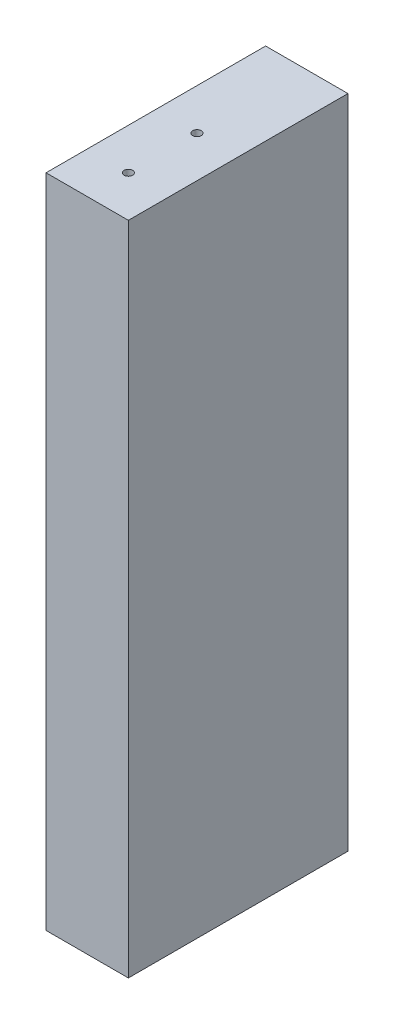
SolidWorks part; units mm, degrees
material "MDF"
ref_plane "Front" through (0, 0, 0) normal (0, 0, 1) x (1, 0, 0)
ref_plane "Top" through (0, 0, 0) normal (0, 1, 0) x (1, 0, 0)
ref_plane "Right" through (0, 0, 0) normal (1, 0, 0) x (0, 0, -1)
sketch "Sketch1" plane through (0, 0, 0) normal (0, 0, 1) x (1, 0, 0)
  line L0 (487.3718, 6450.33) -> (273.05, 6450.33) construction
  line L1 (461.9718, 6450.33) -> (442.9218, 6450.33)
  line L2 (461.9718, 6450.33) -> (461.9718, 6602.1458)
  line L3 (461.9718, 6602.1458) -> (442.9218, 6602.1458)
  line L4 (442.9218, 6450.33) -> (442.9218, 6602.1458)
  line L5 (493.1812, 6602.1458) -> (273.05, 6602.1458) construction
  dimension "D1" = 25.4
  dimension "D2" = 19.05
extrude "Boss-Extrude1" add sketch "Sketch1" along normal blind 50.8
hole_wizard "5/64 (0.07813) Diameter Hole1" positions "Sketch2" profile "Sketch3" hole size "5/64" standard "ANSI Inch"
sketch "Sketch2" plane through (5.6155, 0, -19.05) normal (0, 0, -1) x (-1, 0, 0)
  point P0 (-481.5892, 6993.255)
  point P9 (-386.3392, 6993.255)
  point P18 (-291.0892, 6993.255)
  point P21 (-295.275, 6965.1359)
  point P33 (-295.275, 6812.7359)
  point P45 (-295.275, 6660.3359)
  point P48 (-285.1664, 6631.4688)
  point P66 (-475.4773, 6631.4688)
  point P69 (-485.0023, 6660.3359)
  point P81 (-485.0023, 6812.7359)
  point P93 (-485.0023, 6965.1359)
  point P96 (-478.3656, 6611.6708)
  point P114 (-287.8656, 6611.6708)
  point P117 (-307.975, 6564.3379)
  point P127 (-307.975, 6488.1379)
  point P130 (-284.9609, 6440.805)
  point P143 (-380.2109, 6440.805)
  point P152 (-475.4609, 6440.805)
  point P155 (-446.8313, 6488.1379)
  point P161 (-446.8313, 6564.3379)
  point P164 (-472.2313, 6396.355)
  point P170 (-472.2313, 6320.155)
  point P173 (-472.6532, 6275.705)
  point P182 (-377.4032, 6275.705)
  point P191 (-282.1532, 6275.705)
  point P194 (-282.575, 6320.155)
  point P200 (-282.575, 6396.355)
  point P203 (-435.5986, 6221.73)
  point P209 (-435.5986, 6145.53)
  point P233 (-450.5925, 6091.555)
  point P242 (-460.9986, 6091.5555)
  point P245 (-460.9986, 6056.63)
  point P251 (-460.9986, 5980.43)
  point P263 (-460.9986, 5945.505)
  point P280 (-282.1532, 5945.505)
  point P284 (-368.6118, 5945.505)
sketch "Sketch3" plane through (487.2048, 6993.255, -19.05) normal (1, 0, 0) x (0, 1, 0)
  line L0 (0, 0) -> (0, 38.6962)
  line L1 (0, 38.6962) -> (0.9923, 38.1)
  line L2 (0.9923, 38.1) -> (0.9923, 0)
  line L3 (0.9923, 0) -> (0, 0)
  line L4 (0, 38.6962) -> (-0.9923, 38.1) construction
  line L5 (0, -6.35) -> (0, 107.95) construction
  dimension "Hole Dia." = 1.9845
  dimension "Hole Depth" = 38.1
  dimension "Drill Angle" = 118
hole_wizard "5/64 (0.07813) Diameter Hole2" positions "Sketch4" profile "Sketch5" hole size "5/64" standard "ANSI Inch"
sketch "Sketch4" plane through (144.4718, 0, -19.05) normal (0, 0, -1) x (-1, 0, 0)
  point P0 (-481.5892, 6993.255)
  point P9 (-386.3392, 6993.255)
  point P18 (-291.0892, 6993.255)
  point P21 (-295.275, 6965.1359)
  point P33 (-295.275, 6812.7359)
  point P45 (-295.275, 6660.3359)
  point P48 (-285.1664, 6631.4688)
  point P66 (-475.4773, 6631.4688)
  point P69 (-485.0023, 6660.3359)
  point P81 (-485.0023, 6812.7359)
  point P93 (-485.0023, 6965.1359)
  point P96 (-478.3656, 6611.6708)
  point P114 (-287.8656, 6611.6708)
  point P117 (-307.975, 6564.3379)
  point P127 (-307.975, 6488.1379)
  point P130 (-284.9609, 6440.805)
  point P143 (-380.2109, 6440.805)
  point P152 (-475.4609, 6440.805)
  point P155 (-446.8313, 6488.1379)
  point P161 (-446.8313, 6564.3379)
  point P164 (-472.2313, 6396.355)
  point P170 (-472.2313, 6320.155)
  point P173 (-472.6532, 6275.705)
  point P182 (-377.4032, 6275.705)
  point P191 (-282.1532, 6275.705)
  point P194 (-282.575, 6320.155)
  point P200 (-282.575, 6396.355)
  point P203 (-435.5986, 6221.73)
  point P209 (-435.5986, 6145.53)
  point P233 (-450.5925, 6091.555)
  point P242 (-460.9986, 6091.5555)
  point P245 (-460.9986, 6056.63)
  point P251 (-460.9986, 5980.43)
  point P263 (-460.9986, 5945.505)
  point P280 (-282.1532, 5945.505)
  point P284 (-368.6118, 5945.505)
sketch "Sketch5" plane through (626.0611, 6993.255, -19.05) normal (1, 0, 0) x (0, 1, 0)
  line L0 (0, 0) -> (0, 38.6962)
  line L1 (0, 38.6962) -> (0.9923, 38.1)
  line L2 (0.9923, 38.1) -> (0.9923, 0)
  line L3 (0.9923, 0) -> (0, 0)
  line L4 (0, 38.6962) -> (-0.9923, 38.1) construction
  line L5 (0, -6.35) -> (0, 107.95) construction
  dimension "Hole Dia." = 1.9845
  dimension "Hole Depth" = 38.1
  dimension "Drill Angle" = 118
hole_wizard "5/64 (0.07813) Diameter Hole3" positions "Sketch6" profile "Sketch7" hole size "5/64" standard "ANSI Inch"
sketch "Sketch6" plane through (0, 6602.1458, 0) normal (0, 1, 0) x (1, 0, 0)
  line L0 (452.4468, -50.8) -> (452.4468, 0) construction
  line L1 (461.9718, -50.8) -> (442.9218, -50.8) construction
  line L2 (461.9718, 0) -> (442.9218, 0) construction
  point P8 (452.4468, -25.4)
  point P10 (452.4468, -41.275)
  dimension "D1" = 15.875
sketch "Sketch7" plane through (452.4468, 6602.1458, 41.275) normal (1, 0, 0) x (0, 0, 1)
  line L0 (0, 0) -> (0, 19.6462)
  line L1 (0, 19.6462) -> (0.9923, 19.05)
  line L2 (0.9923, 19.05) -> (0.9923, 0)
  line L5 (0.9923, 0) -> (0, 0)
  line L10 (0, 19.6462) -> (-0.9923, 19.05) construction
  line L11 (0, -6.35) -> (0, 107.95) construction
  dimension "Hole Dia." = 1.9845
  dimension "Hole Depth" = 19.05
  dimension "Drill Angle" = 118
hole_wizard "5/64 (0.07813) Diameter Hole4" positions "Sketch8" profile "Sketch9" hole size "5/64" standard "ANSI Inch"
sketch "Sketch8" plane through (0, 6450.33, 0) normal (0, -1, 0) x (-1, 0, 0)
  circle A0 centre (-452.4468, -41.275) radius 0.9923 construction
  circle A1 centre (-452.4468, -25.4) radius 0.9923 construction
  point P0 (-452.4468, -41.275)
  point P2 (-452.4468, -25.4)
sketch "Sketch9" plane through (452.4468, 6450.33, 41.275) normal (1, 0, 0) x (0, 0, -1)
  line L0 (0, 0) -> (0, 19.6462)
  line L1 (0, 19.6462) -> (0.9923, 19.05)
  line L2 (0.9923, 19.05) -> (0.9923, 0)
  line L5 (0.9923, 0) -> (0, 0)
  line L10 (0, 19.6462) -> (-0.9923, 19.05) construction
  line L11 (0, -6.35) -> (0, 107.95) construction
  dimension "Hole Dia." = 1.9845
  dimension "Hole Depth" = 19.05
  dimension "Drill Angle" = 118
